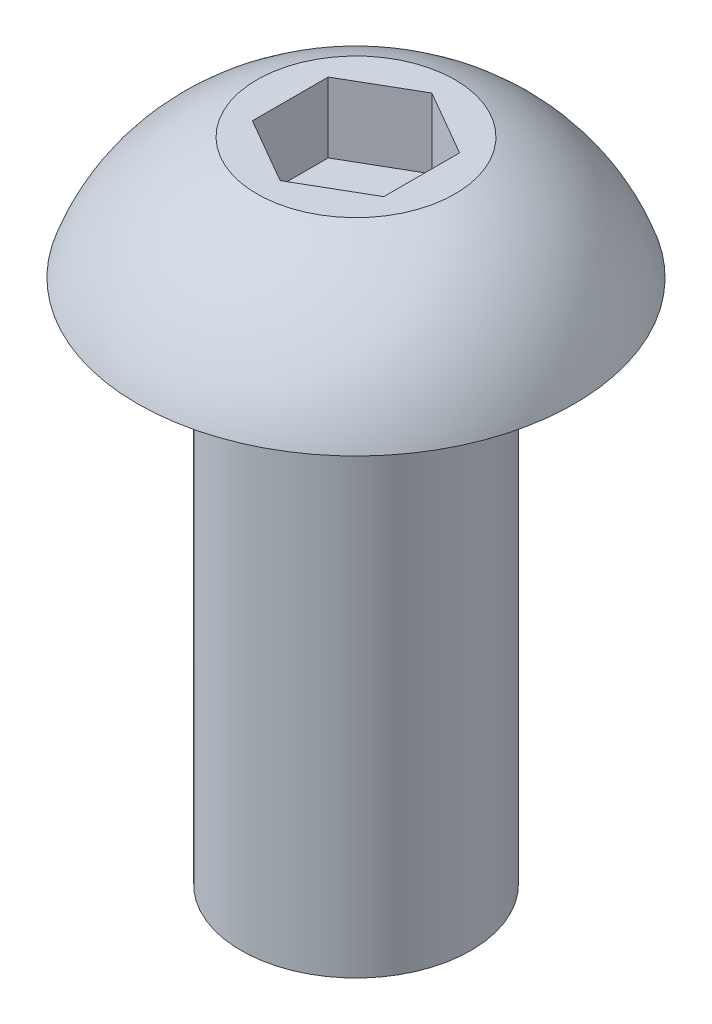
SolidWorks part; units mm, degrees
material "AISI Type 316L stainless steel"
ref_plane "Front Plane" through (0, 0, 0) normal (0, 0, 1) x (1, 0, 0)
ref_plane "Top Plane" through (0, 0, 0) normal (0, 1, 0) x (1, 0, 0)
ref_plane "Right Plane" through (0, 0, 0) normal (1, 0, 0) x (0, 0, -1)
sketch "Sketch1" plane through (0, 0, 0) normal (0, 0, 1) x (1, 0, 0)
  line L0 (-2.0828, 0) -> (-3.9624, 0)
  line L1 (-2.0828, 0) -> (-2.0828, -9.525)
  line L2 (0, -9.525) -> (0, 2.2098)
  line L3 (0, 2.2098) -> (-1.7948, 2.2098)
  line L4 (-2.0828, -9.525) -> (0, -9.525)
  arc A0 (-3.9624, 0) -> (-1.7948, 2.2098) centre (-0.5889, -1.1411) cw
  dimension "D1" = 9.525
  dimension "D2" = 2.2098
  dimension "D3" = 3.9624
  dimension "D4" = 2.0828
  dimension "D5" = 1.7948
revolve "Revolve1" add sketch "Sketch1" angle 360 about L2
sketch "Sketch2" plane through (0, 2.2098, 0) normal (0, 1, 0) x (1, 0, 0)
  line L0 (0, 0) -> (0, 1.3748) construction
  line L1 (-1.1906, 0.6874) -> (-1.1906, -0.6874)
  line L2 (-1.1906, -0.6874) -> (0, -1.3748)
  line L3 (0, -1.3748) -> (1.1906, -0.6874)
  line L4 (1.1906, -0.6874) -> (1.1906, 0.6874)
  line L5 (1.1906, 0.6874) -> (0, 1.3748)
  line L6 (0, 1.3748) -> (-1.1906, 0.6874)
  circle A0 centre (0, 0) radius 1.1906 construction
  dimension "D1" = 2.3813
extrude "Cut-Extrude1" cut sketch "Sketch2" against normal blind 1.27
